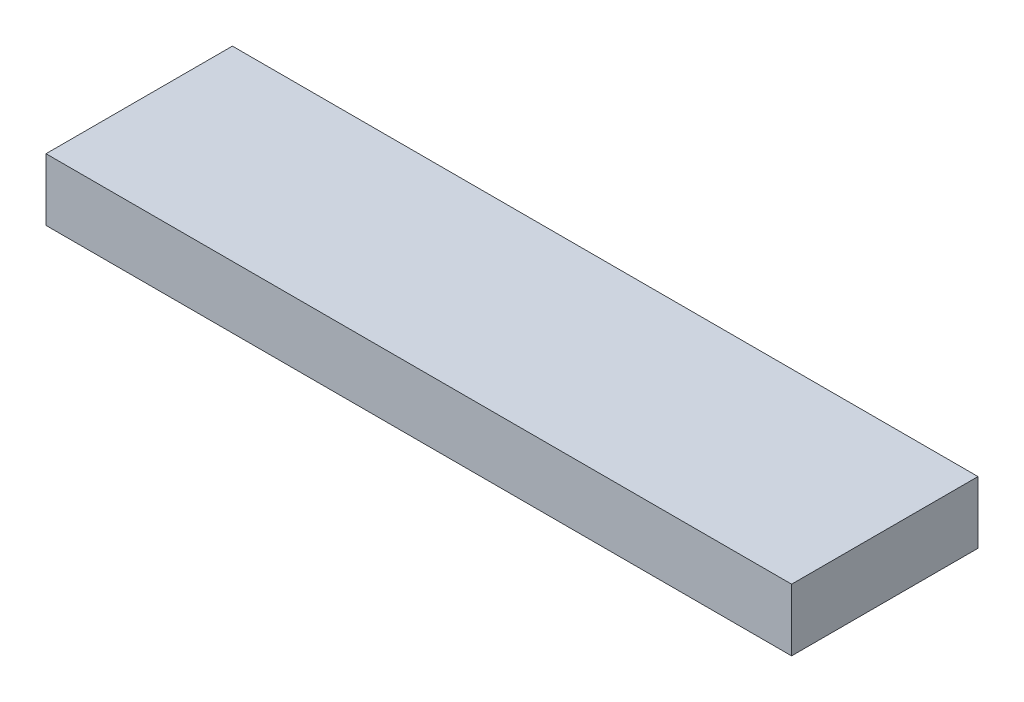
SolidWorks part; units mm, degrees
ref_plane "Front Plane" through (0, 0, 0) normal (0, 0, 1) x (1, 0, 0)
ref_plane "Top Plane" through (0, 0, 0) normal (0, 1, 0) x (1, 0, 0)
ref_plane "Right Plane" through (0, 0, 0) normal (1, 0, 0) x (0, 0, -1)
sketch "Sketch1" plane through (0, 0, 0) normal (0, 1, 0) x (1, 0, 0)
  line L1 (38.1, 9.525) -> (-38.1, 9.525)
  line L2 (38.1, 9.525) -> (38.1, -9.525)
  line L3 (38.1, -9.525) -> (-38.1, -9.525)
  line L4 (-38.1, 9.525) -> (-38.1, -9.525)
  line L5 (38.1, 9.525) -> (-38.1, -9.525) construction
  line L6 (38.1, -9.525) -> (-38.1, 9.525) construction
  point P0 (0, 0)
  dimension "D1" = 19.05
  dimension "D2" = 76.2
extrude "Boss-Extrude1" add sketch "Sketch1" along normal blind 6.35
